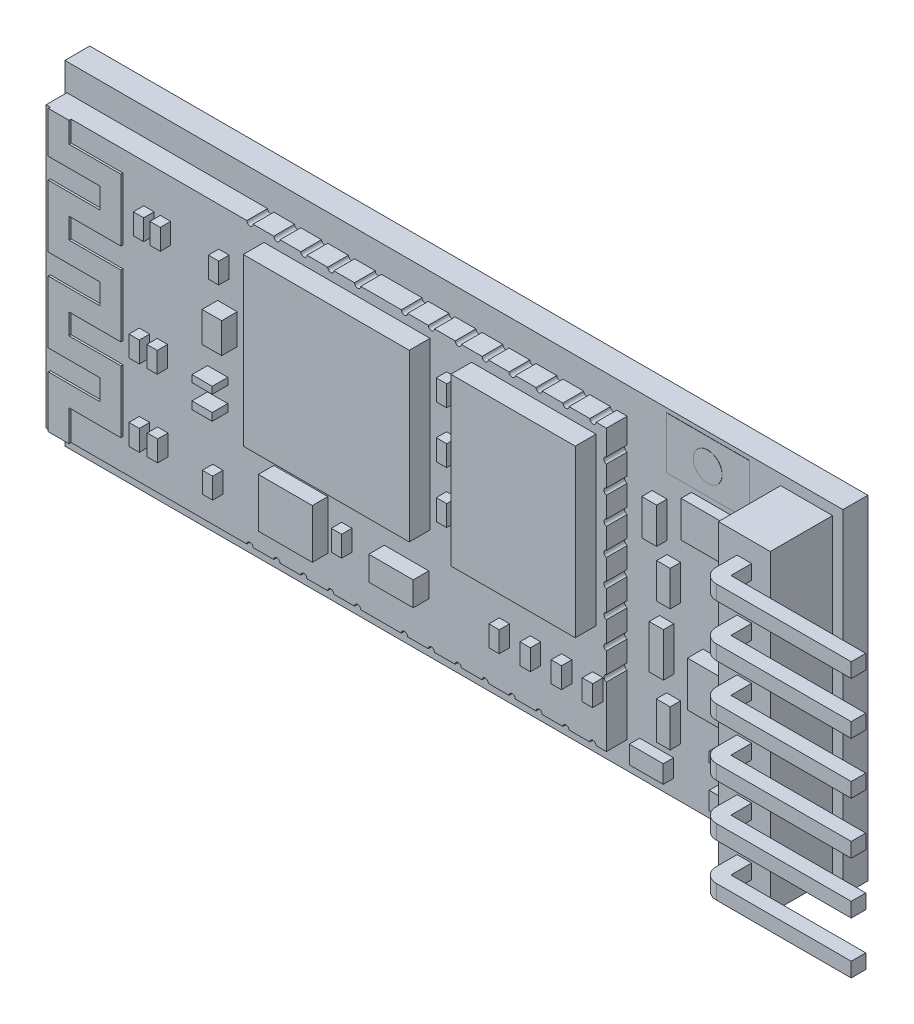
SolidWorks part; units mm, degrees
ref_plane "Ön Düzlem" through (0, 0, 0) normal (0, 0, 1) x (1, 0, 0)
ref_plane "Üst Düzlem" through (0, 0, 0) normal (0, 1, 0) x (1, 0, 0)
ref_plane "Sağ Düzlem" through (0, 0, 0) normal (1, 0, 0) x (0, 0, -1)
sketch "Çizim2" plane through (0, 0, 0) normal (0, 0, 1) x (1, 0, 0)
  line L1 (0, 0) -> (37.5, 0)
  line L2 (0, 0) -> (0, 16.1)
  line L3 (0, 16.1) -> (37.5, 16.1)
  line L4 (37.5, 0) -> (37.5, 16.1)
  dimension "D1" = 37.5
  dimension "D2" = 16.1
extrude "Yükseklik-Ekstrüzyon1" add sketch "Çizim2" along normal blind 1.2
sketch "Çizim5" plane through (0, 0, 1.2) normal (0, 0, 1) x (1, 0, 0)
  line L0 (37.5, 0) -> (37.5, 16.1) construction
  line L1 (34.5, 0.5) -> (37, 0.5)
  line L2 (34.5, 0.5) -> (34.5, 15.6)
  line L3 (34.5, 15.6) -> (37, 15.6)
  line L4 (37, 0.5) -> (37, 15.6)
  line L5 (0, 0) -> (37.5, 0) construction
  line L6 (37.5, 16.1) -> (0, 16.1) construction
  dimension "D1" = 0.5
  dimension "D2" = 0.5
  dimension "D3" = 0.5
  dimension "D4" = 2.5
extrude "Yükseklik-Ekstrüzyon2" add sketch "Çizim5" along normal blind 3
sketch "Çizim6" plane through (0, 0, 4.2) normal (0, 0, 1) x (1, 0, 0)
  line L0 (34.5, 3.05) -> (37, 3.05)
  line L1 (34.5, 15.6) -> (34.5, 0.5) construction
  line L3 (34.5, 5.55) -> (37, 5.55)
  line L4 (37, 0.5) -> (37, 15.6) construction
  line L5 (34.5, 8.05) -> (37, 8.05)
  line L6 (34.5, 10.55) -> (37, 10.55)
  line L7 (34.5, 15.6) -> (34.5, 0.5) construction
  line L8 (34.5, 13.05) -> (37, 13.05)
  line L9 (37, 0.5) -> (37, 15.6) construction
  line L10 (34.5, 0.55) -> (37, 0.55)
  line L11 (34.5, 15.55) -> (37, 15.55)
  line L12 (37, 15.6) -> (34.5, 15.6) construction
  line L13 (34.5, 0.5) -> (37, 0.5) construction
  line L14 (35.4, 4.65) -> (36.1, 4.65)
  line L15 (35.4, 2.15) -> (36.1, 2.15)
  line L16 (35.4, 2.15) -> (35.4, 1.45)
  line L17 (35.4, 1.45) -> (36.1, 1.45)
  line L18 (36.1, 2.15) -> (36.1, 1.45)
  line L19 (35.4, 4.65) -> (35.4, 3.95)
  line L20 (35.4, 3.95) -> (36.1, 3.95)
  line L21 (36.1, 4.65) -> (36.1, 3.95)
  line L22 (35.4, 7.15) -> (36.1, 7.15)
  line L23 (35.4, 7.15) -> (35.4, 6.45)
  line L24 (35.4, 6.45) -> (36.1, 6.45)
  line L25 (36.1, 7.15) -> (36.1, 6.45)
  line L26 (35.4, 12.15) -> (36.1, 12.15)
  line L27 (35.4, 12.15) -> (35.4, 11.45)
  line L28 (35.4, 11.45) -> (36.1, 11.45)
  line L29 (36.1, 12.15) -> (36.1, 11.45)
  line L30 (35.4, 9.65) -> (36.1, 9.65)
  line L31 (35.4, 9.65) -> (35.4, 8.95)
  line L32 (35.4, 8.95) -> (36.1, 8.95)
  line L33 (36.1, 9.65) -> (36.1, 8.95)
  line L34 (35.4, 14.65) -> (36.1, 14.65)
  line L35 (35.4, 14.65) -> (35.4, 13.95)
  line L36 (35.4, 13.95) -> (36.1, 13.95)
  line L37 (36.1, 14.65) -> (36.1, 13.95)
  dimension "D1" = 0.05
  dimension "D2" = 0.05
  dimension "D3" = 2.5
  dimension "D4" = 2.5
  dimension "D5" = 2.5
  dimension "D6" = 2.5
  dimension "D7" = 2.5
  dimension "D8" = 0.7
  dimension "D9" = 0.7
  dimension "D10" = 0.9
  dimension "D11" = 0.9
  dimension "D12" = 0.7
  dimension "D13" = 0.7
  dimension "D14" = 0.9
  dimension "D15" = 0.9
  dimension "D16" = 0.9
  dimension "D17" = 0.9
  dimension "D18" = 0.7
  dimension "D19" = 0.7
  dimension "D20" = 0.9
  dimension "D21" = 0.9
  dimension "D22" = 0.7
  dimension "D23" = 0.7
  dimension "D24" = 0.9
  dimension "D25" = 0.9
  dimension "D26" = 0.7
  dimension "D27" = 0.7
  dimension "D28" = 0.9
  dimension "D29" = 0.7
  dimension "D30" = 0.9
  dimension "D31" = 0.7
extrude "Yükseklik-Ekstrüzyon3" add sketch "Çizim6" along normal blind 1 separate body contours L18 L15 L16 L17 | L21 L14 L19 L20 | L33 L30 L31 L32 | L29 L26 L27 L28 | L37 L34 L35 L36 | L25 L24 L23 L22
sketch "Çizim8" plane through (0, 1.45, 0) normal (0, -1, 0) x (1, 0, 0)
  line L0 (36.1, 5.2) -> (42.6, 5.2)
  line L1 (42.6, 5.2) -> (42.6, 5.9)
  line L2 (42.6, 5.9) -> (36.1, 5.9)
  line L3 (35.4, 5.2) -> (36.1, 5.2)
  arc A0 (36.1, 5.9) -> (35.4, 5.2) centre (36.1, 5.2) ccw
  dimension "D2" = 0.7
  dimension "D1" = 0.7
  dimension "D3" = 6.5
extrude "Yükseklik-Ekstrüzyon4" add sketch "Çizim8" against normal blind 0.7
sketch "Çizim9" plane through (0, 3.95, 0) normal (0, -1, 0) x (1, 0, 0)
  line L0 (36.1, 5.2) -> (42.6, 5.2)
  line L1 (42.6, 5.2) -> (42.6, 5.9)
  line L2 (42.6, 5.9) -> (36.1, 5.9)
  line L3 (36.1, 5.2) -> (35.4, 5.2)
  line L4 (35.4, 5.2) -> (35.4, 4.2) construction
  line L5 (35.4, 5.2) -> (36.1, 5.2) construction
  arc A0 (35.4, 5.2) -> (36.1, 5.9) centre (36.1, 5.2) cw
  dimension "D1" = 6.5
  dimension "D2" = 0.7
  dimension "D3" = 6.5
extrude "Yükseklik-Ekstrüzyon5" add sketch "Çizim9" against normal blind 0.7
sketch "Çizim10" plane through (0, 6.45, 0) normal (0, -1, 0) x (1, 0, 0)
  line L0 (36.1, 5.2) -> (42.6, 5.2)
  line L1 (42.6, 5.2) -> (42.6, 5.9)
  line L2 (42.6, 5.9) -> (36.1, 5.9)
  line L3 (36.1, 5.2) -> (35.4, 5.2)
  arc A0 (35.4, 5.2) -> (36.1, 5.9) centre (36.1, 5.2) cw
extrude "Yükseklik-Ekstrüzyon6" add sketch "Çizim10" against normal blind 0.7
sketch "Çizim11" plane through (0, 8.95, 0) normal (0, -1, 0) x (1, 0, 0)
  line L0 (36.1, 5.2) -> (42.6, 5.2)
  line L1 (42.6, 5.2) -> (42.6, 5.9)
  line L2 (42.6, 5.9) -> (36.1, 5.9)
  line L3 (36.1, 5.2) -> (35.4, 5.2)
  arc A0 (35.4, 5.2) -> (36.1, 5.9) centre (36.1, 5.2) cw
extrude "Yükseklik-Ekstrüzyon7" add sketch "Çizim11" against normal blind 0.7
sketch "Çizim12" plane through (0, 11.45, 0) normal (0, -1, 0) x (1, 0, 0)
  line L0 (36.1, 5.2) -> (42.6, 5.2)
  line L1 (42.6, 5.2) -> (42.6, 5.9)
  line L2 (42.6, 5.9) -> (36.1, 5.9)
  line L3 (36.1, 5.2) -> (35.4, 5.2)
  arc A0 (35.4, 5.2) -> (36.1, 5.9) centre (36.1, 5.2) cw
extrude "Yükseklik-Ekstrüzyon8" add sketch "Çizim12" against normal blind 0.7
sketch "Çizim13" plane through (0, 13.95, 0) normal (0, -1, 0) x (1, 0, 0)
  line L0 (36.1, 5.2) -> (42.6, 5.2)
  line L1 (42.6, 5.2) -> (42.6, 5.9)
  line L2 (42.6, 5.9) -> (36.1, 5.9)
  line L3 (36.1, 5.2) -> (35.4, 5.2)
  arc A0 (35.4, 5.2) -> (36.1, 5.9) centre (36.1, 5.2) cw
extrude "Yükseklik-Ekstrüzyon9" add sketch "Çizim13" against normal blind 0.7
sketch "Çizim14" plane through (0, 0, 1.2) normal (0, 0, 1) x (1, 0, 0)
  line L1 (0.1, 14.8) -> (27.1, 14.8)
  line L2 (0.1, 14.8) -> (0.1, 1.3)
  line L3 (0.1, 1.3) -> (27.1, 1.3)
  line L4 (27.1, 14.8) -> (27.1, 1.3)
  line L5 (37.5, 16.1) -> (0, 16.1) construction
  line L7 (0, 16.1) -> (0, 0) construction
  point P6 (0, 8.05)
  dimension "D1" = 13.5
  dimension "D2" = 27
  dimension "D3" = 1.3
  dimension "D4" = 0.1
extrude "Yükseklik-Ekstrüzyon10" add sketch "Çizim14" along normal blind 1
sketch "Çizim15" plane through (0, 0, 2.2) normal (0, 0, 1) x (1, 0, 0)
  line L0 (0.3, 1.3) -> (0.3, 14.8) construction
  line L1 (0.1, 1.3) -> (27.1, 1.3) construction
  line L2 (27.1, 14.8) -> (0.1, 14.8) construction
  line L3 (0.1, 14.8) -> (0.1, 1.3) construction
  line L4 (3.8, 14.8) -> (3.8, 1.3) construction
  line L5 (0.3, 1.3) -> (0.3, 3.8)
  line L6 (1.3, 2.8) -> (3.8, 2.8)
  line L7 (3.8, 2.8) -> (3.8, 5.8)
  line L8 (0.3, 3.8) -> (2.8, 3.8)
  line L9 (1.3, 1.3) -> (1.3, 2.8)
  line L10 (0.1, 1.3) -> (27.1, 1.3) construction
  line L11 (2.8, 3.8) -> (2.8, 4.8)
  line L12 (2.8, 4.8) -> (0.3, 4.8)
  line L13 (0.3, 4.8) -> (0.3, 7.8)
  line L14 (0.3, 7.8) -> (2.8, 7.8)
  line L15 (3.8, 5.8) -> (1.3, 5.8)
  line L16 (1.3, 5.8) -> (1.3, 6.8)
  line L17 (1.3, 6.8) -> (3.8, 6.8)
  line L18 (3.8, 6.8) -> (3.8, 9.8)
  line L19 (2.8, 7.8) -> (2.8, 8.8)
  line L20 (2.8, 8.8) -> (0.3, 8.8)
  line L21 (0.3, 8.8) -> (0.3, 11.8)
  line L22 (3.8, 9.8) -> (1.3, 9.8)
  line L23 (1.3, 9.8) -> (1.3, 10.8)
  line L24 (1.3, 10.8) -> (3.8, 10.8)
  line L25 (3.8, 10.8) -> (3.8, 13.8)
  line L26 (0.3, 11.8) -> (2.8, 11.8)
  line L27 (2.8, 11.8) -> (2.8, 12.8)
  line L28 (2.8, 12.8) -> (0.3, 12.8)
  line L29 (0.3, 12.8) -> (0.3, 14.8)
  line L30 (3.8, 13.8) -> (1.3, 13.8)
  line L31 (1.3, 13.8) -> (1.3, 14.8)
  line L32 (1.3, 14.8) -> (0.3, 14.8)
  line L33 (1.3, 1.3) -> (0.3, 1.3)
  dimension "D1" = 0.2
  dimension "D2" = 3.5
  dimension "D3" = 2.5
  dimension "D4" = 1
  dimension "D5" = 1.5
  dimension "D6" = 3
  dimension "D7" = 1
  dimension "D8" = 1
  dimension "D9" = 1
  dimension "D10" = 1
  dimension "D11" = 1
  dimension "D12" = 2.5
  dimension "D13" = 3
  dimension "D14" = 2.5
  dimension "D15" = 3
  dimension "D16" = 1
  dimension "D17" = 1
  dimension "D18" = 1
  dimension "D19" = 2.5
  dimension "D20" = 2.5
  dimension "D21" = 1
  dimension "D22" = 3
  dimension "D23" = 1
extrude "Yükseklik-Ekstrüzyon11" add sketch "Çizim15" along normal blind 0.1
sketch "Çizim16" plane through (0, 0, 1.2) normal (0, 0, 1) x (1, 0, 0)
  line L0 (37.5, 16.1) -> (0, 16.1) construction
  line L1 (29, 15.9) -> (33, 15.9)
  line L2 (29, 15.9) -> (29, 13.4)
  line L3 (29, 13.4) -> (33, 13.4)
  line L4 (33, 15.9) -> (33, 13.4)
  line L5 (34.5, 15.6) -> (34.5, 0.5) construction
  dimension "D1" = 2.5
  dimension "D2" = 4
  dimension "D3" = 0.2
  dimension "D4" = 1.5
extrude "Yükseklik-Ekstrüzyon12" add sketch "Çizim16" along normal blind 0.01 separate body
sketch "Çizim17" plane through (0, 0, 1.21) normal (0, 0, 1) x (1, 0, 0)
  line L0 (29, 14.65) -> (33, 14.65) construction
  line L1 (29, 15.9) -> (29, 13.4) construction
  line L2 (33, 13.4) -> (33, 15.9) construction
  line L3 (31, 15.9) -> (31, 13.4) construction
  line L4 (33, 15.9) -> (29, 15.9) construction
  line L5 (29, 13.4) -> (33, 13.4) construction
  circle A0 centre (31, 14.65) radius 0.6936
extrude "Yükseklik-Ekstrüzyon13" add sketch "Çizim17" along normal blind 0.01
sketch "Çizim18" plane through (0, 0, 2.2) normal (0, 0, 1) x (1, 0, 0)
  line L0 (27.1, 14.8) -> (1.3, 14.8) construction
  line L1 (26.6004, 6.3) -> (20.6004, 6.3)
  line L2 (26.6004, 6.3) -> (26.6004, 14.3)
  line L3 (26.6004, 14.3) -> (20.6004, 14.3)
  line L4 (20.6004, 6.3) -> (20.6004, 14.3)
  line L5 (27.1, 1.3) -> (27.1, 14.8) construction
  line L7 (18.6004, 6.3) -> (10.6004, 6.3)
  line L8 (18.6004, 6.3) -> (18.6004, 14.3)
  line L9 (18.6004, 14.3) -> (10.6004, 14.3)
  line L10 (10.6004, 6.3) -> (10.6004, 14.3)
  dimension "D1" = 8
  dimension "D2" = 6
  dimension "D3" = 0.5
  dimension "D4" = 0.4996
  dimension "D5" = 2
  dimension "D6" = 8
  dimension "D7" = 8
  dimension "D8" = 0.5
extrude "Yükseklik-Ekstrüzyon14" add sketch "Çizim18" along normal blind 1
sketch "Çizim19" plane through (0, 0, 2.2) normal (0, 0, 1) x (1, 0, 0)
  line L0 (3.8, 10.8) -> (3.8, 13.8) construction
  line L1 (4.8, 11.93) -> (5.3, 11.93)
  line L2 (4.8, 11.93) -> (4.8, 12.93)
  line L3 (4.8, 12.93) -> (5.3, 12.93)
  line L4 (5.3, 11.93) -> (5.3, 12.93)
  line L5 (5.6, 11.93) -> (6.1, 11.93)
  line L6 (5.6, 11.93) -> (5.6, 12.93)
  line L7 (5.6, 12.93) -> (6.1, 12.93)
  line L8 (6.1, 11.93) -> (6.1, 12.93)
  line L9 (8.4157, 11.93) -> (8.9157, 11.93)
  line L10 (8.4157, 11.93) -> (8.4157, 12.93)
  line L11 (8.4157, 12.93) -> (8.9157, 12.93)
  line L12 (8.9157, 11.93) -> (8.9157, 12.93)
  dimension "D1" = 1
  dimension "D2" = 0.5
  dimension "D3" = 1
  dimension "D4" = 0.5
  dimension "D5" = 1
  dimension "D6" = 0.5
  dimension "D7" = 1
  dimension "D8" = 0.3
extrude "Yükseklik-Ekstrüzyon15" add sketch "Çizim19" along normal blind 0.5
sketch "Çizim22" plane through (0, 0, 2.2) normal (0, 0, 1) x (1, 0, 0)
  line L0 (4.589, 6.722) -> (5.089, 6.722)
  line L1 (4.589, 6.722) -> (4.589, 7.722)
  line L2 (4.589, 7.722) -> (5.089, 7.722)
  line L3 (5.089, 6.722) -> (5.089, 7.722)
  line L4 (5.4516, 6.722) -> (5.9516, 6.722)
  line L5 (5.4516, 6.722) -> (5.4516, 7.722)
  line L6 (5.4516, 7.722) -> (5.9516, 7.722)
  line L7 (5.9516, 6.722) -> (5.9516, 7.722)
  line L8 (4.5888, 3.0335) -> (5.0888, 3.0335)
  line L9 (4.5888, 3.0335) -> (4.5888, 4.0335)
  line L10 (4.5888, 4.0335) -> (5.0888, 4.0335)
  line L11 (5.0888, 3.0335) -> (5.0888, 4.0335)
  line L12 (5.4701, 3.0335) -> (5.9701, 3.0335)
  line L13 (5.4701, 3.0335) -> (5.4701, 4.0335)
  line L14 (5.4701, 4.0335) -> (5.9701, 4.0335)
  line L15 (5.9701, 3.0335) -> (5.9701, 4.0335)
  line L16 (8.1243, 2.8062) -> (8.6243, 2.8062)
  line L17 (8.1243, 2.8062) -> (8.1243, 3.8062)
  line L18 (8.1243, 3.8062) -> (8.6243, 3.8062)
  line L19 (8.6243, 2.8062) -> (8.6243, 3.8062)
  line L20 (19.4004, 12.3) -> (19.9004, 12.3)
  line L21 (19.4004, 12.3) -> (19.4004, 13.3)
  line L22 (19.4004, 13.3) -> (19.9004, 13.3)
  line L23 (19.9004, 12.3) -> (19.9004, 13.3)
  line L24 (19.4004, 9.8) -> (19.9004, 9.8)
  line L25 (19.4004, 9.8) -> (19.4004, 10.8)
  line L26 (19.4004, 10.8) -> (19.9004, 10.8)
  line L27 (19.9004, 9.8) -> (19.9004, 10.8)
  line L28 (19.9004, 7.3) -> (19.4004, 7.3)
  line L29 (19.9004, 7.3) -> (19.9004, 8.3)
  line L30 (19.9004, 8.3) -> (19.4004, 8.3)
  line L31 (19.4004, 7.3) -> (19.4004, 8.3)
  line L32 (26.4351, 3.3) -> (26.9351, 3.3)
  line L33 (26.4351, 3.3) -> (26.4351, 4.3)
  line L34 (26.4351, 4.3) -> (26.9351, 4.3)
  line L35 (26.9351, 3.3) -> (26.9351, 4.3)
  line L36 (24.9351, 3.3) -> (25.4351, 3.3)
  line L37 (24.9351, 3.3) -> (24.9351, 4.3)
  line L38 (24.9351, 4.3) -> (25.4351, 4.3)
  line L39 (25.4351, 3.3) -> (25.4351, 4.3)
  line L40 (23.4351, 3.3) -> (23.9351, 3.3)
  line L41 (23.4351, 3.3) -> (23.4351, 4.3)
  line L42 (23.4351, 4.3) -> (23.9351, 4.3)
  line L43 (23.9351, 3.3) -> (23.9351, 4.3)
  line L44 (21.9351, 3.3) -> (22.4351, 3.3)
  line L45 (21.9351, 3.3) -> (21.9351, 4.3)
  line L46 (21.9351, 4.3) -> (22.4351, 4.3)
  line L47 (22.4351, 3.3) -> (22.4351, 4.3)
  line L48 (14.3404, 3.4908) -> (14.8404, 3.4908)
  line L49 (14.3404, 3.4908) -> (14.3404, 4.4908)
  line L50 (14.3404, 4.4908) -> (14.8404, 4.4908)
  line L51 (14.8404, 3.4908) -> (14.8404, 4.4908)
  line L52 (27.1, 14.8) -> (1.3, 14.8) construction
  line L54 (20.6004, 14.3) -> (20.6004, 6.3) construction
  line L55 (20.6004, 6.3) -> (26.6004, 6.3) construction
  dimension "D1" = 1
  dimension "D2" = 1
  dimension "D3" = 1
  dimension "D4" = 1
  dimension "D5" = 1
  dimension "D6" = 1
  dimension "D7" = 1
  dimension "D8" = 1
  dimension "D9" = 1
  dimension "D10" = 1
  dimension "D11" = 1
  dimension "D12" = 1
  dimension "D13" = 1
  dimension "D14" = 0.5
  dimension "D15" = 0.5
  dimension "D16" = 0.5
  dimension "D17" = 1.5
  dimension "D18" = 1.5
  dimension "D19" = 1.5
  dimension "D20" = 0.7
  dimension "D21" = 2
  dimension "D22" = 1
  dimension "D23" = 1
  dimension "D24" = 1
  dimension "D25" = 0.5
  dimension "D26" = 0.5
  dimension "D27" = 0.5
  dimension "D28" = 0.5
extrude "Yükseklik-Ekstrüzyon17" add sketch "Çizim22" along normal blind 0.5
sketch "Çizim23" plane through (0, 0, 2.2) normal (0, 0, 1) x (1, 0, 0)
  line L1 (11.0751, 2.8642) -> (13.6775, 2.8642)
  line L2 (11.0751, 2.8642) -> (11.0751, 5.2317)
  line L3 (11.0751, 5.2317) -> (13.6775, 5.2317)
  line L4 (13.6775, 2.8642) -> (13.6775, 5.2317)
  line L6 (16.3989, 3.3962) -> (18.5402, 3.3962)
  line L7 (16.3989, 3.3962) -> (16.3989, 4.5627)
  line L8 (16.3989, 4.5627) -> (18.5402, 4.5627)
  line L9 (18.5402, 3.3962) -> (18.5402, 4.5627)
  line L10 (7.8761, 6.3372) -> (8.8522, 6.3372)
  line L11 (7.8761, 6.3372) -> (7.8761, 6.7031)
  line L12 (7.8761, 6.7031) -> (8.8522, 6.7031)
  line L13 (8.8522, 6.3372) -> (8.8522, 6.7031)
  line L14 (7.8761, 7.4637) -> (8.8522, 7.4637)
  line L15 (7.8761, 7.4637) -> (7.8761, 7.7984)
  line L16 (7.8761, 7.7984) -> (8.8522, 7.7984)
  line L17 (8.8522, 7.4637) -> (8.8522, 7.7984)
  line L18 (8.3641, 9.3029) -> (9.3075, 9.3029)
  line L19 (8.3641, 9.3029) -> (8.3641, 10.7632)
  line L20 (8.3641, 10.7632) -> (9.3075, 10.7632)
  line L21 (9.3075, 9.3029) -> (9.3075, 10.7632)
extrude "Yükseklik-Ekstrüzyon18" add sketch "Çizim23" along normal blind 0.75
sketch "Çizim24" plane through (0, 0, 1.2) normal (0, 0, 1) x (1, 0, 0)
  line L1 (30.2001, 11.4276) -> (32.9069, 11.4276)
  line L2 (30.2001, 11.4276) -> (30.2001, 13.1705)
  line L3 (30.2001, 13.1705) -> (32.9069, 13.1705)
  line L4 (32.9069, 11.4276) -> (32.9069, 13.1705)
  line L5 (28.3044, 10.5724) -> (29.0208, 10.5724)
  line L6 (28.3044, 10.5724) -> (28.3044, 12.2991)
  line L7 (28.3044, 12.2991) -> (29.0208, 12.2991)
  line L8 (29.0208, 10.5724) -> (29.0208, 12.2991)
  line L9 (29.0208, 8.2903) -> (29.6736, 8.2903)
  line L10 (29.0208, 8.2903) -> (29.0208, 9.9841)
  line L11 (29.0208, 9.9841) -> (29.6736, 9.9841)
  line L12 (29.6736, 8.2903) -> (29.6736, 9.9841)
  line L13 (28.6626, 5.1548) -> (29.3472, 5.1548)
  line L14 (28.6626, 5.1548) -> (28.6626, 7.2612)
  line L15 (28.6626, 7.2612) -> (29.3472, 7.2612)
  line L16 (29.3472, 5.1548) -> (29.3472, 7.2612)
  line L17 (29.0049, 2.403) -> (29.6736, 2.403)
  line L18 (29.0049, 2.403) -> (29.0049, 4.2038)
  line L19 (29.0049, 4.2038) -> (29.6736, 4.2038)
  line L20 (29.6736, 2.403) -> (29.6736, 4.2038)
  line L21 (27.7053, 0.8007) -> (29.3393, 0.8007)
  line L22 (27.7053, 0.8007) -> (27.7053, 1.6631)
  line L23 (27.7053, 1.6631) -> (29.3393, 1.6631)
  line L24 (29.3393, 0.8007) -> (29.3393, 1.6631)
  line L25 (31.5535, 0.8007) -> (32.9069, 0.8007)
  line L26 (31.5535, 0.8007) -> (31.5535, 1.6631)
  line L27 (31.5535, 1.6631) -> (32.9069, 1.6631)
  line L28 (32.9069, 0.8007) -> (32.9069, 1.6631)
  line L29 (31.5535, 2.804) -> (32.9069, 2.804)
  line L30 (31.5535, 2.804) -> (31.5535, 3.3034)
  line L31 (31.5535, 3.3034) -> (32.9069, 3.3034)
  line L32 (32.9069, 2.804) -> (32.9069, 3.3034)
  line L33 (32.0202, 10.8077) -> (33.3885, 10.8077)
  line L34 (32.0202, 10.8077) -> (32.0202, 9.9841)
  line L35 (32.0202, 9.9841) -> (33.3885, 9.9841)
  line L36 (33.3885, 10.8077) -> (33.3885, 9.9841)
  line L37 (32.0202, 8.2903) -> (33.3885, 8.2903)
  line L38 (32.0202, 8.2903) -> (32.0202, 9.082)
  line L39 (32.0202, 9.082) -> (33.3885, 9.082)
  line L40 (33.3885, 8.2903) -> (33.3885, 9.082)
extrude "Yükseklik-Ekstrüzyon19" add sketch "Çizim24" along normal blind 0.5
sketch "Çizim25" plane through (0, 0, 1.2) normal (0, 0, 1) x (1, 0, 0)
  line L1 (30.7569, 4.7405) -> (33.8081, 4.7405)
  line L2 (30.7569, 4.7405) -> (30.7569, 6.9062)
  line L3 (30.7569, 6.9062) -> (33.8081, 6.9062)
  line L4 (33.8081, 4.7405) -> (33.8081, 6.9062)
extrude "Yükseklik-Ekstrüzyon20" add sketch "Çizim25" along normal blind 0.75
sketch "Çizim27" plane through (0, 0, 2.2) normal (0, 0, 1) x (1, 0, 0)
  line L0 (27.1, 14.8) -> (1.3, 14.8) construction
  line L1 (27.1, 1.3) -> (27.1, 14.8) construction
  line L2 (26.6, 14.8) -> (26.3, 14.8)
  line L3 (25.3, 14.8) -> (25.0045, 14.8)
  line L4 (24.5045, 14.4582) -> (24.5045, 15.2412) construction
  line L5 (23.7089, 14.8) -> (24.0045, 14.8)
  line L6 (22.4089, 14.8) -> (22.7089, 14.8)
  line L7 (21.9089, 14.5317) -> (21.9089, 15.1738) construction
  line L8 (21.4089, 14.8) -> (21.1089, 14.8)
  line L9 (20.1089, 14.8) -> (19.8134, 14.8)
  line L10 (18.5179, 14.8) -> (18.8134, 14.8)
  line L11 (17.2179, 14.8) -> (17.5179, 14.8)
  line L12 (16.2399, 14.5317) -> (16.2399, 15.1738) construction
  line L13 (10.5708, 14.5317) -> (10.5708, 15.1738) construction
  line L14 (15.2619, 14.8) -> (14.9619, 14.8)
  line L15 (13.9619, 14.8) -> (13.6663, 14.8)
  line L16 (12.3708, 14.8) -> (12.6663, 14.8)
  line L17 (11.0708, 14.8) -> (11.3708, 14.8)
  line L18 (10.0708, 14.8) -> (9.7708, 14.8)
  line L19 (27.1, 8.05) -> (0.1, 8.05) construction
  line L20 (0.1, 14.8) -> (0.1, 1.3) construction
  line L21 (10.5708, 1.5683) -> (10.5708, 0.9262) construction
  line L22 (16.2399, 1.5683) -> (16.2399, 0.9262) construction
  line L23 (21.9089, 1.5683) -> (21.9089, 0.9262) construction
  line L24 (24.5045, 1.6418) -> (24.5045, 0.8588) construction
  line L25 (10.0708, 1.3) -> (9.7708, 1.3)
  line L26 (11.0708, 1.3) -> (11.3708, 1.3)
  line L27 (12.3708, 1.3) -> (12.6663, 1.3)
  line L28 (13.9619, 1.3) -> (13.6663, 1.3)
  line L29 (15.2619, 1.3) -> (14.9619, 1.3)
  line L30 (17.2179, 1.3) -> (17.5179, 1.3)
  line L31 (18.5179, 1.3) -> (18.8134, 1.3)
  line L32 (20.1089, 1.3) -> (19.8134, 1.3)
  line L33 (21.4089, 1.3) -> (21.1089, 1.3)
  line L34 (22.4089, 1.3) -> (22.7089, 1.3)
  line L35 (23.7089, 1.3) -> (24.0045, 1.3)
  line L36 (25.3, 1.3) -> (25.0045, 1.3)
  line L37 (26.6, 1.3) -> (26.3, 1.3)
  arc A0 (26.6, 14.8) -> (26.3, 14.8) centre (26.45, 14.8) cw
  arc A1 (25.3, 14.8) -> (25.0045, 14.8) centre (25.1522, 14.8) cw
  arc A2 (23.7089, 14.8) -> (24.0045, 14.8) centre (23.8567, 14.8) ccw
  arc A3 (22.4089, 14.8) -> (22.7089, 14.8) centre (22.5589, 14.8) ccw
  arc A4 (21.4089, 14.8) -> (21.1089, 14.8) centre (21.2589, 14.8) cw
  arc A5 (20.1089, 14.8) -> (19.8134, 14.8) centre (19.9612, 14.8) cw
  arc A6 (18.5179, 14.8) -> (18.8134, 14.8) centre (18.6656, 14.8) ccw
  arc A7 (17.2179, 14.8) -> (17.5179, 14.8) centre (17.3679, 14.8) ccw
  arc A8 (15.2619, 14.8) -> (14.9619, 14.8) centre (15.1119, 14.8) cw
  arc A9 (13.9619, 14.8) -> (13.6663, 14.8) centre (13.8141, 14.8) cw
  arc A10 (12.3708, 14.8) -> (12.6663, 14.8) centre (12.5186, 14.8) ccw
  arc A11 (11.0708, 14.8) -> (11.3708, 14.8) centre (11.2208, 14.8) ccw
  arc A12 (10.0708, 14.8) -> (9.7708, 14.8) centre (9.9208, 14.8) cw
  arc A13 (10.0708, 1.3) -> (9.7708, 1.3) centre (9.9208, 1.3) ccw
  arc A14 (11.0708, 1.3) -> (11.3708, 1.3) centre (11.2208, 1.3) cw
  arc A15 (12.3708, 1.3) -> (12.6663, 1.3) centre (12.5186, 1.3) cw
  arc A16 (13.9619, 1.3) -> (13.6663, 1.3) centre (13.8141, 1.3) ccw
  arc A17 (15.2619, 1.3) -> (14.9619, 1.3) centre (15.1119, 1.3) ccw
  arc A18 (17.2179, 1.3) -> (17.5179, 1.3) centre (17.3679, 1.3) cw
  arc A19 (18.5179, 1.3) -> (18.8134, 1.3) centre (18.6656, 1.3) cw
  arc A20 (20.1089, 1.3) -> (19.8134, 1.3) centre (19.9612, 1.3) ccw
  arc A21 (21.4089, 1.3) -> (21.1089, 1.3) centre (21.2589, 1.3) ccw
  arc A22 (22.4089, 1.3) -> (22.7089, 1.3) centre (22.5589, 1.3) cw
  arc A23 (23.7089, 1.3) -> (24.0045, 1.3) centre (23.8567, 1.3) cw
  arc A24 (25.3, 1.3) -> (25.0045, 1.3) centre (25.1522, 1.3) ccw
  arc A25 (26.6, 1.3) -> (26.3, 1.3) centre (26.45, 1.3) ccw
  dimension "D1" = 0.5
  dimension "D2" = 0.3
  dimension "D3" = 1
  dimension "D4" = 0.5
  dimension "D5" = 0.5
extrude "Kes-Ekstrüzyon1" cut sketch "Çizim27" against normal blind 1
sketch "Çizim28" plane through (0, 0, 2.2) normal (0, 0, 1) x (1, 0, 0)
  line L0 (27.1, 1.3) -> (27.1, 14.8) construction
  line L1 (27.1, 13.3005) -> (27.1, 13.5998)
  line L2 (26.7694, 12.8005) -> (27.3012, 12.8005) construction
  line L3 (27.1, 12.3005) -> (27.1, 12.0011)
  line L4 (26.8075, 11.5011) -> (27.3621, 11.5011) construction
  line L5 (27.1, 10.7018) -> (27.1, 11.0011)
  line L6 (27.1, 9.7018) -> (27.1, 9.4024)
  line L7 (26.7694, 8.9024) -> (27.3621, 8.9024) construction
  line L8 (27.3621, 8.9024) -> (27.0657, 8.9024) construction
  line L9 (26.8075, 6.3037) -> (27.3621, 6.3037) construction
  line L10 (26.7694, 5.0044) -> (27.3012, 5.0044) construction
  line L11 (27.1, 8.1031) -> (27.1, 8.4024)
  line L12 (27.1, 7.1031) -> (27.1, 6.8037)
  line L13 (27.1, 5.5044) -> (27.1, 5.8037)
  line L14 (27.1, 4.5044) -> (27.1, 4.205)
  arc A0 (27.1, 13.5998) -> (27.1, 13.3005) centre (27.1317, 13.4502) ccw
  arc A1 (27.1, 12.0011) -> (27.1, 12.3005) centre (27.1317, 12.1508) cw
  arc A2 (27.1, 11.0011) -> (27.1, 10.7018) centre (27.1317, 10.8514) ccw
  arc A3 (27.1, 9.4024) -> (27.1, 9.7018) centre (27.1317, 9.5521) cw
  arc A4 (27.1, 8.4024) -> (27.1, 8.1031) centre (27.1317, 8.2527) ccw
  arc A5 (27.1, 6.8037) -> (27.1, 7.1031) centre (27.1317, 6.9534) cw
  arc A6 (27.1, 5.8037) -> (27.1, 5.5044) centre (27.1317, 5.654) ccw
  arc A7 (27.1, 4.205) -> (27.1, 4.5044) centre (27.1317, 4.3547) cw
  dimension "D1" = 0.5
  dimension "D2" = 0.5
  dimension "D3" = 0.5
extrude "Kes-Ekstrüzyon2" cut sketch "Çizim28" against normal blind 1
